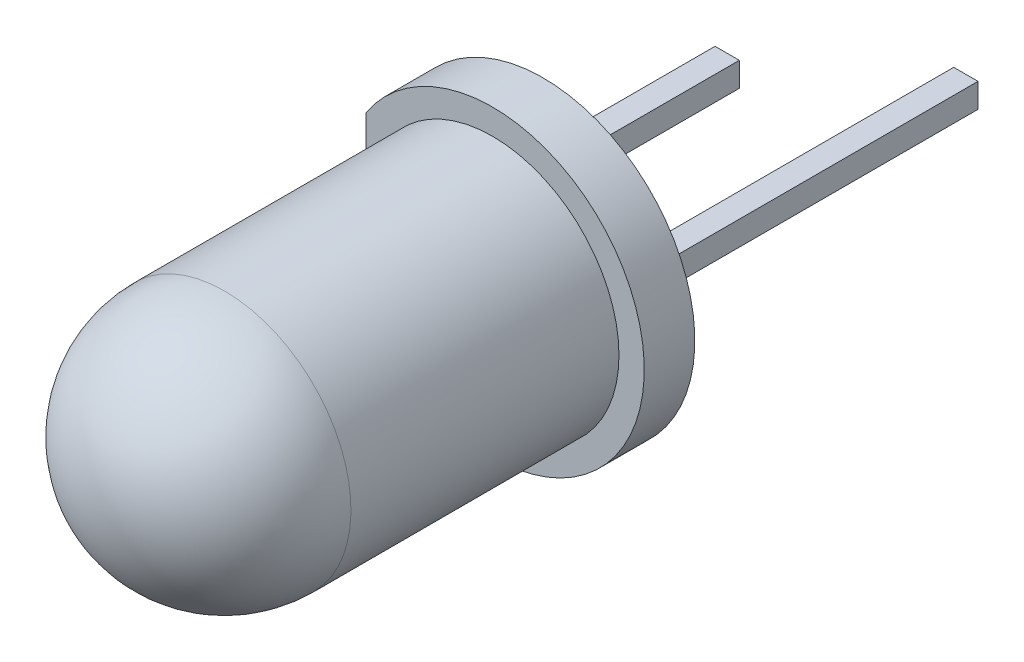
SolidWorks part; units mm, degrees
material "ABS"
ref_plane "Front Plane" through (0, 0, 0) normal (0, 0, 1) x (1, 0, 0)
ref_plane "Top Plane" through (0, 0, 0) normal (0, 1, 0) x (1, 0, 0)
ref_plane "Right Plane" through (0, 0, 0) normal (1, 0, 0) x (0, 0, -1)
sketch "Sketch1" plane through (0, 0, 0) normal (0, 0, 1) x (1, 0, 0)
  circle A0 centre (0, 0) radius 3
  dimension "D1" = 6
extrude "Boss-Extrude1" add sketch "Sketch1" along normal blind 1
sketch "Sketch2" plane through (0, 0, 0) normal (1, 0, 0) x (0, 0, -1)
  line L0 (-1, 0) -> (-8.8, 0)
  line L1 (-1, 3) -> (-1, -3) construction
  line L2 (-6.3, 2.5) -> (-1, 2.5)
  line L3 (-1, 0) -> (-1, 2.5)
  arc A0 (-8.8, 0) -> (-6.3, 2.5) centre (-6.3, 0) cw
  dimension "D1" = 2.5
  dimension "D2" = 7.8
revolve "Revolve1" add sketch "Sketch2" angle 360 about L0
sketch "Sketch3" plane through (0, 0, 0) normal (0, 0, -1) x (-1, 0, 0)
  line L0 (2.5, 1.6583) -> (2.5, -1.6583)
  circle A0 centre (0, 0) radius 3 construction
  arc A1 (2.5, -1.6583) -> (2.5, 1.6583) centre (0, 0) ccw
  circle A2 centre (0, 0) radius 2.5 construction
extrude "Cut-Extrude1" cut sketch "Sketch3" against normal up to surface (1 mm away) up to face at (2.5, 0, 1)
sketch "Sketch4" plane through (0, 0, 0) normal (0, 0, -1) x (-1, 0, 0)
  line L0 (-1.12, 0) -> (1.12, 0) construction
  line L1 (-1.6, -0.24) -> (-1.12, -0.24)
  line L2 (-1.6, -0.24) -> (-1.6, 0.24)
  line L3 (-1.6, 0.24) -> (-1.12, 0.24)
  line L4 (-1.12, -0.24) -> (-1.12, 0.24)
  line L5 (1.12, -0.24) -> (1.6, -0.24)
  line L6 (1.12, -0.24) -> (1.12, 0.24)
  line L7 (1.12, 0.24) -> (1.6, 0.24)
  line L8 (1.6, -0.24) -> (1.6, 0.24)
  dimension "D1" = 3.2
  dimension "D2" = 0.48
extrude "Boss-Extrude2" add sketch "Sketch4" along normal blind 5 separate body
sketch "Sketch5" plane through (0, 0, -5) normal (0, 0, -1) x (-1, 0, 0)
  line L4 (-1.6, 0.24) -> (-1.6, -0.24)
  line L5 (-1.6, -0.24) -> (-1.12, -0.24)
  line L6 (-1.12, -0.24) -> (-1.12, 0.24)
  line L7 (-1.12, 0.24) -> (-1.6, 0.24)
  line L8 (-1.6, 0.24) -> (-1.6, -0.24)
  line L9 (-1.6, -0.24) -> (-1.12, -0.24)
  line L10 (-1.12, -0.24) -> (-1.12, 0.24)
  line L11 (-1.12, 0.24) -> (-1.6, 0.24)
  dimension "D1" = 0
extrude "Boss-Extrude3" add sketch "Sketch5" along normal blind 2 separate body
sketch "Sketch6" plane through (0, 0, 0) normal (0, 1, 0) x (1, 0, 0)
  line L0 (-1.6, 0) -> (-1.6, -3.5)
  line L1 (-1.12, 0) -> (-1.12, -2)
  line L2 (0.02, -2) -> (1.2, -4)
  line L3 (1.2, -4) -> (-1.3, -4)
  line L4 (-1.3, -4) -> (-1.6, -3.5)
  line L5 (-1.12, -2) -> (0.02, -2)
  line L6 (1.6, 0) -> (1.6, -4)
  line L7 (1.6, -4) -> (1.4, -4)
  line L8 (1.4, -4) -> (0.22, -2)
  line L9 (0.22, -2) -> (1.12, -2)
  line L10 (1.12, -2) -> (1.12, 0)
  line L11 (-1.6, 0) -> (-1.12, 0)
  line L12 (1.12, 0) -> (1.6, 0)
  dimension "D1" = 4
  dimension "D2" = 2
  dimension "D3" = 2.8
  dimension "D4" = 0.2
  dimension "D5" = 0.9
  dimension "D6" = 3.5
  dimension "D7" = 2.5
extrude "Cut-Extrude2" cut sketch "Sketch6" against normal mid plane 0.48
sketch "Sketch7" plane through (0, 0, 0) normal (0, 1, 0) x (1, 0, 0)
  line L0 (-1.3, -4) -> (1.2, -4) construction
  line L1 (-1.6, -3.5) -> (-1.3, -4) construction
  line L2 (-1.6, 0) -> (-1.6, -3.5) construction
  line L3 (1.2, -4) -> (0.02, -2) construction
  line L4 (0.02, -2) -> (-1.12, -2) construction
  line L5 (-1.12, -2) -> (-1.12, 0) construction
  line L6 (0.22, -2) -> (1.4, -4) construction
  line L7 (1.12, -2) -> (0.22, -2) construction
  line L8 (1.12, 0) -> (1.12, -2) construction
  line L9 (1.6, -4) -> (1.6, 0) construction
  line L10 (1.4, -4) -> (1.6, -4) construction
  line L11 (-1.12, 0) -> (-1.6, 0) construction
  line L12 (1.6, 0) -> (1.12, 0) construction
  line L13 (-1.3, -4) -> (1.2, -4)
  line L14 (-1.6, -3.5) -> (-1.3, -4)
  line L15 (-1.6, 0) -> (-1.6, -3.5)
  line L16 (1.2, -4) -> (0.02, -2)
  line L17 (0.02, -2) -> (-1.12, -2)
  line L18 (-1.12, -2) -> (-1.12, 0)
  line L19 (0.22, -2) -> (1.4, -4)
  line L20 (1.12, -2) -> (0.22, -2)
  line L21 (1.12, 0) -> (1.12, -2)
  line L22 (1.6, -4) -> (1.6, 0)
  line L23 (1.4, -4) -> (1.6, -4)
  line L24 (-1.12, 0) -> (-1.6, 0)
  line L25 (1.6, 0) -> (1.12, 0)
extrude "Boss-Extrude4" add sketch "Sketch7" along normal mid plane 0.48 separate body
combine bodies "Combine1" operation type add bodies to combine 109 106 104
combine bodies "Combine2" operation type add bodies to combine 108 105
sketch "Sketch8" plane through (0, 0, 0) normal (0, 1, 0) x (1, 0, 0)
  line L0 (-0.05, -4) -> (-0.05, -3.7)
  line L1 (-1.3, -4) -> (1.2, -4) construction
  line L2 (-0.55, -4) -> (-0.05, -4)
  arc A0 (-0.05, -3.7) -> (-0.55, -4) centre (-0.05, -4.2667) ccw
  dimension "D1" = 0.5
  dimension "D2" = 0.3
revolve "Cut-Revolve1" cut sketch "Sketch8" angle 360 about L0
sketch "Sketch9" plane through (0, 0, 0) normal (0, 1, 0) x (1, 0, 0)
  line L0 (-0.55, -4) -> (-0.05, -4) construction
  line L1 (-0.05, -4) -> (-0.05, -3.7) construction
  line L2 (-0.55, -4) -> (-0.05, -4)
  line L3 (-0.05, -4) -> (-0.05, -3.7)
  arc A0 (-0.05, -3.7) -> (-0.55, -4) centre (-0.05, -4.2667) ccw construction
  arc A1 (-0.05, -3.7) -> (-0.55, -4) centre (-0.05, -4.2667) ccw
revolve "Revolve2" add sketch "Sketch9" angle 360 about L3
combine bodies "Combine3" operation type add bodies to combine 113 112
sketch "Sketch10" plane through (0, 0, 4) normal (0, 0, 1) x (1, 0, 0)
  circle A0 centre (-0.05, 0) radius 0.2
  arc A1 (0.3886, 0.24) -> (-0.4886, 0.24) centre (-0.05, 0) ccw construction
  dimension "D1" = 0.4
extrude "Cut-Extrude3" cut sketch "Sketch10" against normal blind 0.1
sketch "Sketch11" plane through (0, 0, 0) normal (0, 1, 0) x (1, 0, 0)
  line L0 (1.6, 7) -> (-7.0603, 12)
  line L1 (1.6, 7) -> (1.12, 7) construction
  dimension "D1" = 10
  dimension "D2" = 30
ref_plane "Plane1" through (3.4311, 0, -5.9428) normal (0.5, 0, -0.866) x (-0.866, 0, -0.5)
